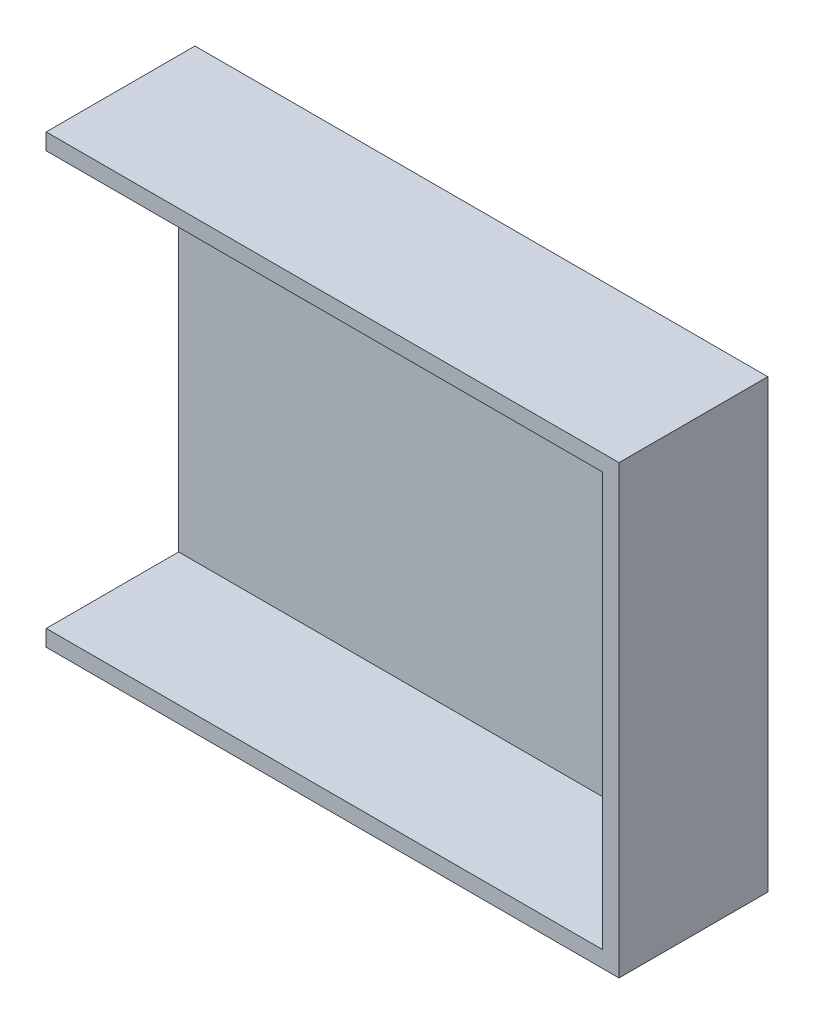
SolidWorks part; units mm, degrees
ref_plane "Front Plane" through (0, 0, 0) normal (1, 0, 0) x (0, 1, 0)
ref_plane "Top Plane" through (0, 0, 0) normal (0, 0, 1) x (0, 1, 0)
ref_plane "Right Plane" through (0, 0, 0) normal (0, 1, 0) x (-1, 0, 0)
sketch "Sketch2" plane through (0, 0, 0) normal (0, 0, 1) x (0, 1, 0)
  line L1 (-38.1, -79.6422) -> (-190.5, -79.6422)
  line L2 (-38.1, -79.6422) -> (-38.1, 115.9378)
  line L3 (-38.1, 115.9378) -> (-190.5, 115.9378)
  line L4 (-190.5, -79.6422) -> (-190.5, 115.9378)
  line L5 (-38.1, -79.6422) -> (-190.5, 115.9378) construction
  line L6 (-38.1, 115.9378) -> (-190.5, -79.6422) construction
  point P0 (-114.3, 18.1478)
  dimension "D1" = 152.4
  dimension "D2" = 195.58
extrude "Boss-Extrude1" add sketch "Sketch2" along normal blind 50.8
shell "Shell1" thickness 5.588
